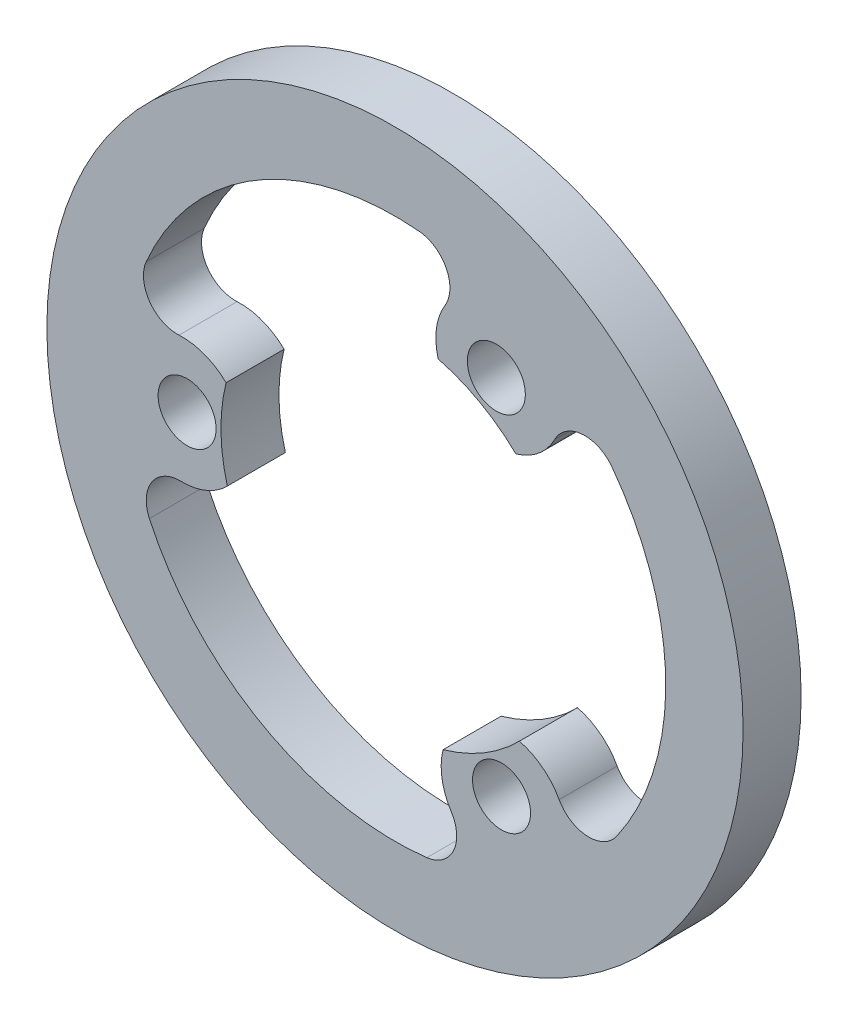
SolidWorks part; units mm, degrees
ref_plane "Plan de face" through (0, 0, 0) normal (0, 0, 1) x (1, 0, 0)
ref_plane "Plan de dessus" through (0, 0, 0) normal (0, 1, 0) x (1, 0, 0)
ref_plane "Plan de droite" through (0, 0, 0) normal (1, 0, 0) x (0, 0, -1)
sketch "Esquisse1" plane through (0, 0, 0) normal (0, 0, 1) x (1, 0, 0)
  line L0 (5.2405, 9.3862) -> (0, 0) construction
  circle A0 centre (0, 0) radius 18
  circle A9 centre (5.2405, 9.3862) radius 1.5
  circle A19 centre (0, 0) radius 7.75 construction
  arc A21 (2.4856, -8.65) -> (6.4322, -6.295) centre (0, 0) ccw
  arc A22 (11.4536, -8.0507) -> (11.2172, 8.3771) centre (0, 0) ccw
  arc A25 (8.487, -7.885) -> (11.4536, -8.0507) centre (10.0219, -7.0444) ccw
  arc A28 (2.5851, 11.2925) -> (2.2356, 8.7179) centre (5.3623, 9.6045) ccw
  arc A29 (2.5851, 11.2925) -> (1.2453, 13.9445) centre (1.0897, 12.2014) ccw
  arc A30 (11.2172, 8.3771) -> (8.2566, 8.126) centre (9.815, 7.3299) ccw
  arc A31 (1.2453, 13.9445) -> (-12.8633, 5.5258) centre (0, 0) ccw
  arc A32 (-12.699, -5.8938) -> (1.6462, -13.9029) centre (0, 0) ccw
  arc A33 (6.2483, 6.4775) -> (8.2566, 8.126) centre (5.3623, 9.6045) ccw
  arc A34 (-8.7339, 2.1724) -> (-11.1656, 3.0874) centre (-10.9989, -0.1583) ccw
  arc A35 (2.4856, -8.65) -> (2.909, -11.2134) centre (5.6365, -9.4461) ccw
  circle A36 centre (5.5084, -9.2314) radius 1.5
  arc A37 (8.487, -7.885) -> (6.4322, -6.295) centre (5.6365, -9.4461) ccw
  arc A38 (1.6462, -13.9029) -> (2.909, -11.2134) centre (1.4404, -12.165) ccw
  arc A39 (-11.0721, -3.4075) -> (-12.699, -5.8938) centre (-11.1116, -5.157) ccw
  circle A40 centre (-10.7489, -0.1547) radius 1.5
  arc A41 (-11.0721, -3.4075) -> (-8.6677, -2.4229) centre (-10.9989, -0.1583) ccw
  arc A42 (-12.8633, 5.5258) -> (-11.1656, 3.0874) centre (-11.2554, 4.8351) ccw
  arc A43 (6.2483, 6.4775) -> (2.2356, 8.7179) centre (0, 0) ccw
  arc A44 (-8.7339, 2.1724) -> (-8.6677, -2.4229) centre (0, 0) ccw
  circle A45 centre (0, 0) radius 9 construction
  point P32 (0, 0)
  point P37 (0, 0)
  point P49 (0, 0)
  dimension "D1" = 36
  dimension "D2" = 10.7489
  dimension "D3" = 3
  dimension "D5" = 15.5
  dimension "D7" = 18
  dimension "D14" = 28
  dimension "D6" = 10.75
extrude "Boss.-Extru.1" add sketch "Esquisse1" along normal blind 3
